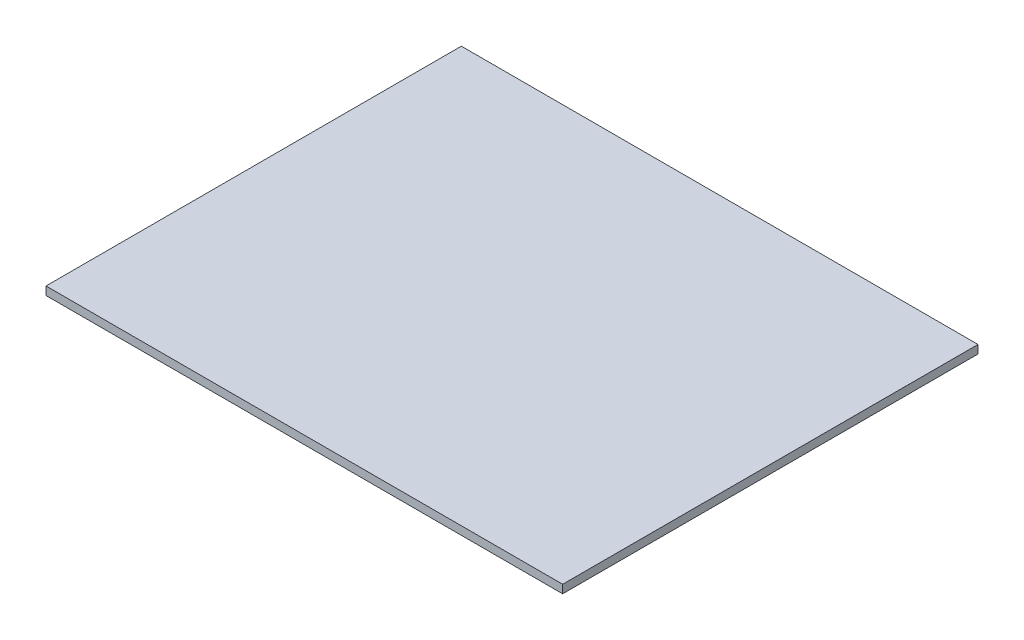
SolidWorks part; units mm, degrees
material "PVC Rigid"
ref_plane "Front Plane" through (0, 0, 0) normal (0, 0, 1) x (1, 0, 0)
ref_plane "Top Plane" through (0, 0, 0) normal (0, 1, 0) x (1, 0, 0)
ref_plane "Right Plane" through (0, 0, 0) normal (1, 0, 0) x (0, 0, -1)
sketch "Sketch1" plane through (0, 241.45, 0) normal (0, 1, 0) x (1, 0, 0)
  line L1 (355.7875, -14.224) -> (-39.6875, -14.224)
  line L2 (355.7875, -14.224) -> (355.7875, 303.699)
  line L3 (355.7875, 303.699) -> (-39.6875, 303.699)
  line L4 (-39.6875, -14.224) -> (-39.6875, 303.699)
extrude "Boss-Extrude1" add sketch "Sketch1" along normal blind 6.35
